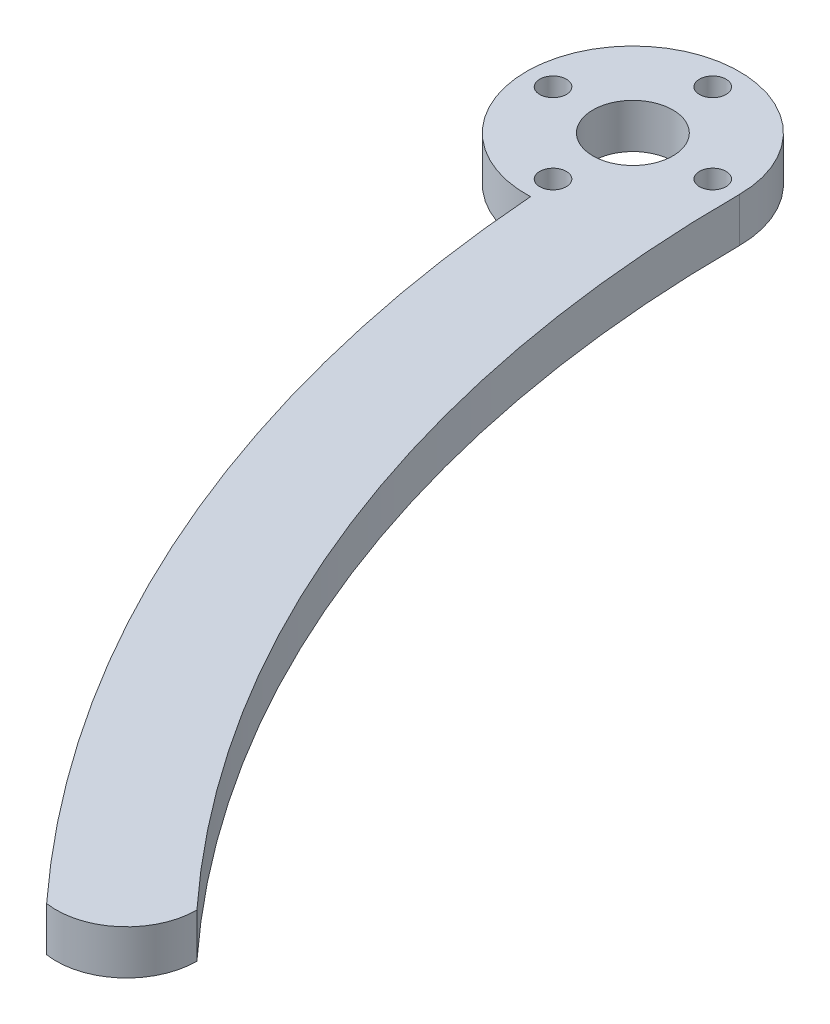
SolidWorks part; units mm, degrees
material "Balsa"
ref_plane "Plan de face" through (0, 0, 0) normal (0, 0, 1) x (1, 0, 0)
ref_plane "Plan de dessus" through (0, 0, 0) normal (0, 1, 0) x (1, 0, 0)
ref_plane "Plan de droite" through (0, 0, 0) normal (1, 0, 0) x (0, 0, -1)
sketch "Esquisse1" plane through (0, 0, 0) normal (0, 1, 0) x (1, 0, 0)
  line L0 (-65.2777, 0) -> (58.012, 0) construction
  line L2 (0, 0) -> (-123.9203, -114.4513) construction
  line L5 (-108.7232, -100.4155) -> (-124.5662, -100.4155) construction
  circle A0 centre (0, 0) radius 90 construction
  circle A1 centre (-160, 0) radius 4.5
  circle A2 centre (-160, 0) radius 12 construction
  arc A3 (-148, 0) -> (-159.55, -11.9916) centre (-160, 0) ccw
  arc A4 (-108.7232, -100.4155) -> (-148, 0) centre (0, 0) cw
  arc A5 (-159.55, -11.9916) -> (-117.8226, -108.2489) centre (0, 0) ccw
  arc A6 (-108.7232, -100.4155) -> (-117.8226, -108.2489) centre (-116.6447, -100.4155) cw
  dimension "D1" = 180
  dimension "D5" = 9
  dimension "D6" = 24
  dimension "D4" = 160
extrude "Boss.-Extru.1" add sketch "Esquisse1" along normal blind 5
sketch "Esquisse2" plane through (0, 5, 0) normal (0, 1, 0) x (1, 0, 0)
  circle A0 centre (-151, 0) radius 1.5
  circle A1 centre (-160, -9) radius 1.5
  circle A2 centre (-169, 0) radius 1.5
  circle A3 centre (-160, 9) radius 1.5
  circle A4 centre (-160, 0) radius 4.5 construction
  point P13 (-160, 0)
  dimension "D1" = 3
  dimension "D2" = 4
  dimension "D3" = 0
  dimension "D5" = 9
extrude "Enlèv. mat.-Extru.1" cut sketch "Esquisse2" against normal blind 5
